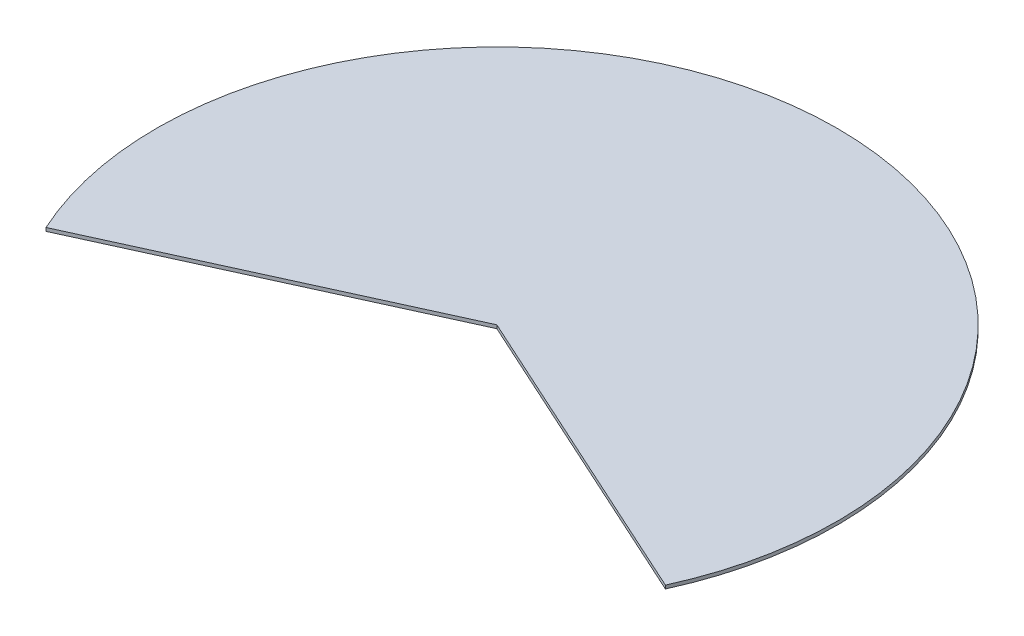
SolidWorks part; units mm, degrees
ref_plane "Front Plane" through (0, 0, 0) normal (0, 0, 1) x (1, 0, 0)
ref_plane "Top Plane" through (0, 0, 0) normal (0, 1, 0) x (1, 0, 0)
ref_plane "Right Plane" through (0, 0, 0) normal (1, 0, 0) x (0, 0, -1)
sketch "Sketch1" plane through (0, 0, 0) normal (0, 1, 0) x (1, 0, 0)
  line L0 (-909.9613, -414.6932) -> (0, 0)
  line L1 (0, 0) -> (909.9613, -414.6932)
  arc A0 (-909.9613, -414.6932) -> (909.9613, -414.6932) centre (0, 0) cw
  dimension "D1" = 1000
  dimension "D2" = 229
extrude "Boss-Extrude1" add sketch "Sketch1" along normal blind 10
